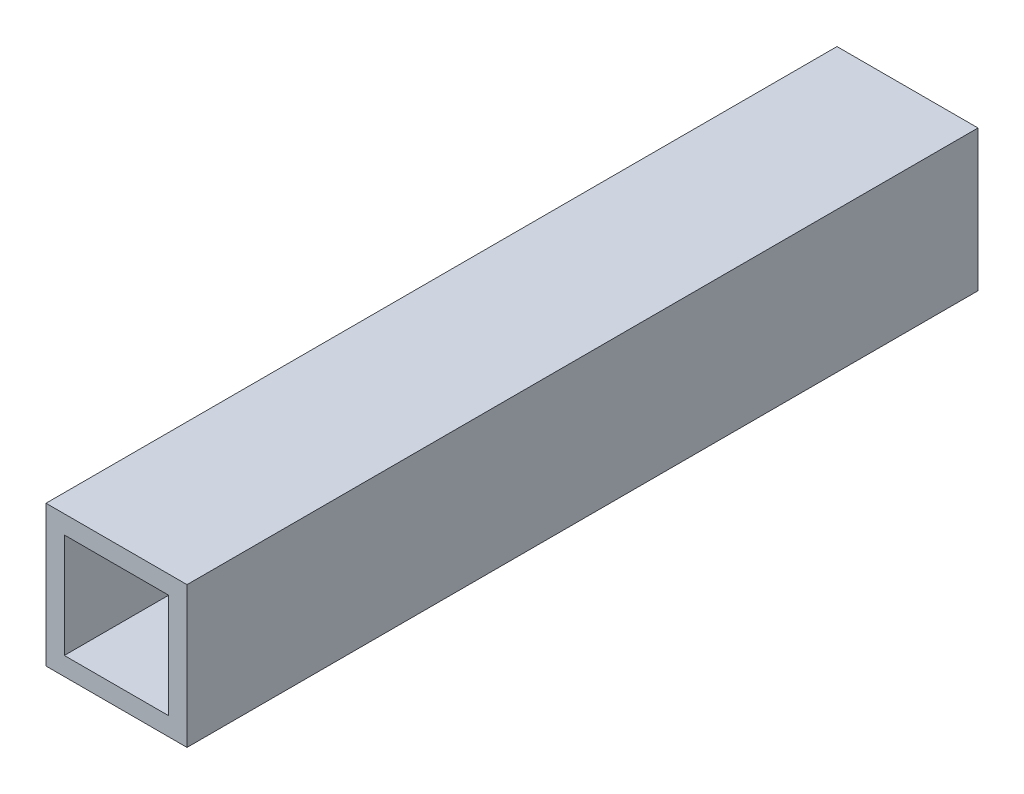
SolidWorks part; units mm, degrees
ref_plane "Front Plane" through (0, 0, 0) normal (0, 0, 1) x (1, 0, 0)
ref_plane "Top Plane" through (0, 0, 0) normal (0, 1, 0) x (1, 0, 0)
ref_plane "Right Plane" through (0, 0, 0) normal (1, 0, 0) x (0, 0, -1)
sketch "Sketch1" plane through (0, 0, 0) normal (0, 0, 1) x (1, 0, 0)
  line L1 (6.35, 6.35) -> (-6.35, 6.35)
  line L2 (6.35, 6.35) -> (6.35, -6.35)
  line L3 (6.35, -6.35) -> (-6.35, -6.35)
  line L4 (-6.35, 6.35) -> (-6.35, -6.35)
  line L5 (6.35, 6.35) -> (-6.35, -6.35) construction
  line L6 (6.35, -6.35) -> (-6.35, 6.35) construction
  line L7 (4.7, 4.7) -> (-4.7, 4.7)
  line L8 (4.7, 4.7) -> (4.7, -4.7)
  line L9 (4.7, -4.7) -> (-4.7, -4.7)
  line L10 (-4.7, 4.7) -> (-4.7, -4.7)
  line L11 (4.7, 4.7) -> (-4.7, -4.7) construction
  line L12 (4.7, -4.7) -> (-4.7, 4.7) construction
  point P0 (0, 0)
  point P5 (0, 0)
  dimension "D1" = 12.7
  dimension "D2" = 9.4
extrude "Boss-Extrude1" add sketch "Sketch1" along normal blind 71.24
